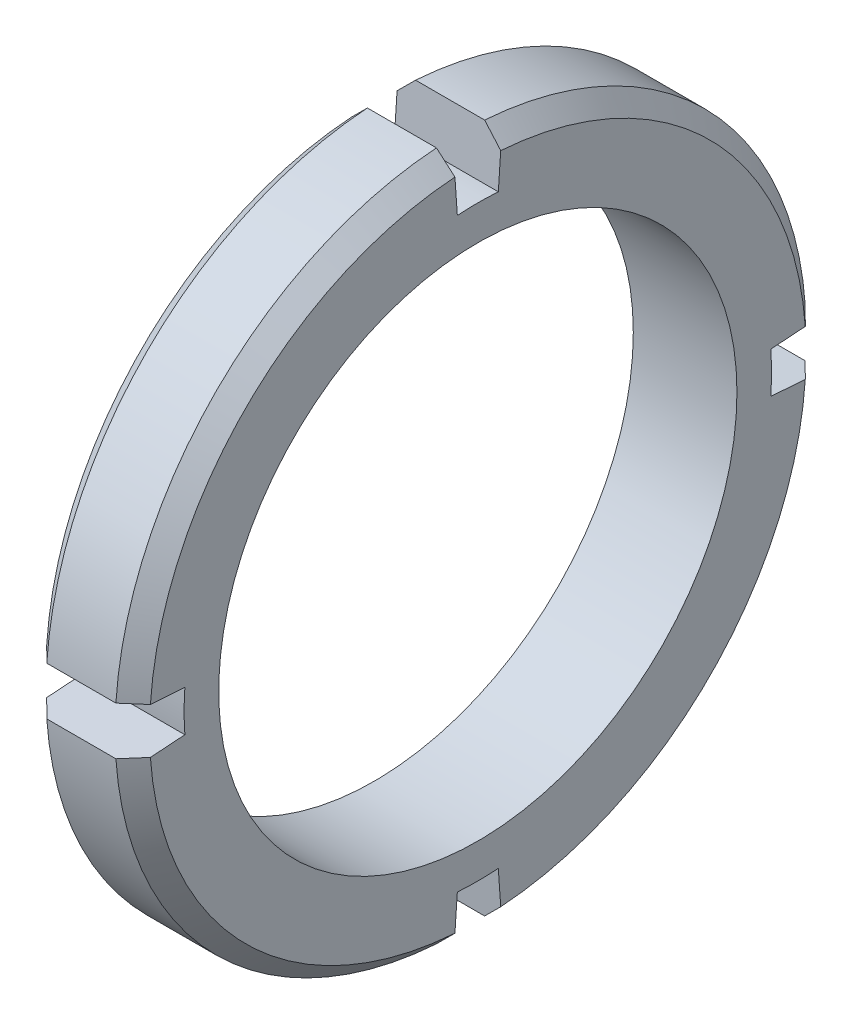
SolidWorks part; units mm, degrees
ref_plane "前视基准面" through (0, 0, 0) normal (0, 0, 1) x (1, 0, 0)
ref_plane "上视基准面" through (0, 0, 0) normal (0, 1, 0) x (1, 0, 0)
ref_plane "右视基准面" through (0, 0, 0) normal (1, 0, 0) x (0, 0, -1)
sketch "草图1" plane through (0, 0, 0) normal (1, 0, 0) x (0, 0, -1)
  circle A0 centre (0, 0) radius 15
  circle A1 centre (0, 0) radius 20
extrude "凸台-拉伸1" add sketch "草图1" along normal blind 6
chamfer "倒角1" distance 1 angle 45 2 edges at (0, 0, -20) (6, 0, -20)
sketch "草图2" plane through (6, 0, 0) normal (1, 0, 0) x (0, 0, -1)
  line L1 (16.9586, -1.1859) -> (20.7475, -1.4508)
  line L2 (16.9586, 1.1859) -> (20.7475, 1.4508)
  arc A0 (20.7475, -1.4508) -> (20.7475, 1.4508) centre (0, 0) ccw
  arc A1 (16.9586, -1.1859) -> (16.9586, 1.1859) centre (0, 0) ccw
extrude "切除-拉伸1" cut sketch "草图2" against normal blind 10
pattern_circular "阵列(圆周)1" count 4 over 360 about axis through (6, 0, 0) along (1, 0, 0) of "切除-拉伸1"
